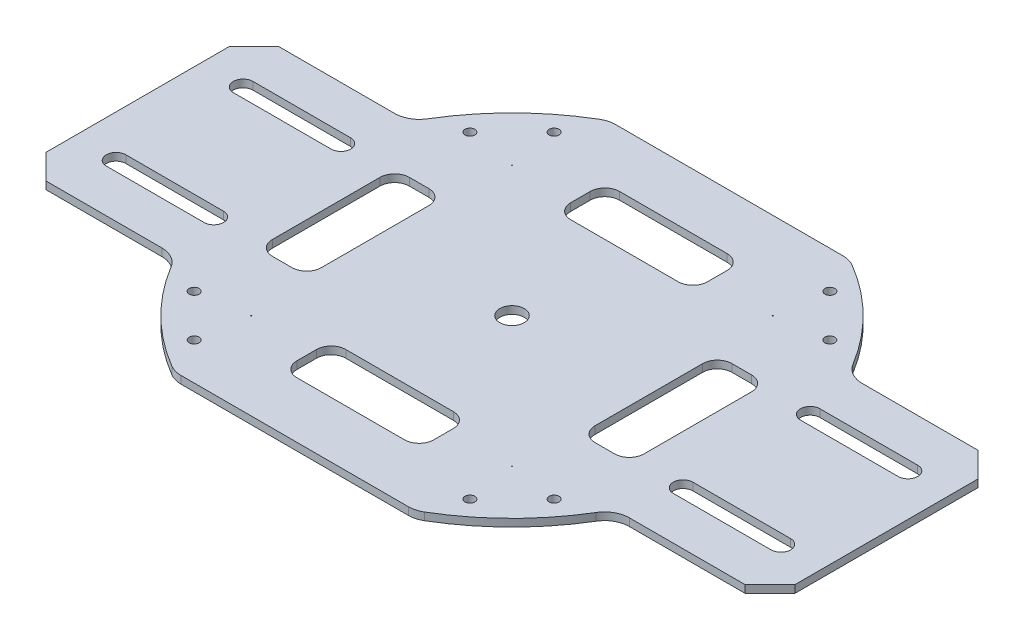
SolidWorks part; units mm, degrees
ref_plane "Front Plane" through (0, 0, 0) normal (0, 0, 1) x (1, 0, 0)
ref_plane "Top Plane" through (0, 0, 0) normal (0, 1, 0) x (1, 0, 0)
ref_plane "Right Plane" through (0, 0, 0) normal (1, 0, 0) x (0, 0, -1)
sketch "Sketch1" plane through (0, 0, 0) normal (0, 1, 0) x (1, 0, 0)
  line L0 (0, -1000) -> (0, 49000) construction
  line L1 (-23.2448, 44.45) -> (23.2448, 44.45)
  line L2 (-76.5969, 18.7325) -> (-76.5969, -18.7325)
  line L3 (-23.2448, -44.45) -> (23.2448, -44.45)
  line L4 (76.5969, 18.7325) -> (76.5969, -18.7325)
  line L6 (35.4178, 36.4243) -> (41.9684, 29.8736) construction
  line L7 (-76.5969, 0) -> (76.5969, 0) construction
  line L8 (-71.5169, 23.8125) -> (-47.8309, 23.8125)
  line L9 (-71.5169, -23.8125) -> (-47.8309, -23.8125)
  line L10 (-23.8125, 64.7529) -> (-23.8125, -44.45) construction
  line L11 (23.8125, 64.7529) -> (23.8125, -44.45) construction
  line L12 (47.8309, -23.8125) -> (71.5169, -23.8125)
  line L13 (47.8309, 23.8125) -> (71.5169, 23.8125)
  line L14 (-76.5969, -18.7325) -> (-71.5169, -23.8125)
  line L15 (-71.5169, 23.8125) -> (-76.5969, 18.7325)
  line L16 (71.5169, 23.8125) -> (76.5969, 18.7325)
  line L17 (71.5169, -23.8125) -> (76.5969, -18.7325)
  line L18 (707.1068, -707.1068) -> (-34648.2323, 34648.2323) construction
  line L19 (-707.1068, -707.1068) -> (34648.2323, 34648.2323) construction
  circle A0 centre (0, 0) radius 2.5
  arc A1 (-25.8276, 43.7444) -> (-43.4827, 26.2659) centre (0, 0) ccw
  arc A2 (25.8276, 43.7444) -> (23.2448, 44.45) centre (23.2448, 39.37) ccw
  arc A3 (-23.2448, 44.45) -> (-25.8276, 43.7444) centre (-23.2448, 39.37) ccw
  arc A4 (25.8276, -43.7444) -> (43.4827, -26.2659) centre (0, 0) ccw
  arc A5 (25.8276, -43.7444) -> (23.2448, -44.45) centre (23.2448, -39.37) cw
  arc A6 (-25.8276, -43.7444) -> (-23.2448, -44.45) centre (-23.2448, -39.37) ccw
  arc A7 (-43.4827, -26.2659) -> (-25.8276, -43.7444) centre (0, 0) ccw
  arc A8 (43.4827, 26.2659) -> (25.8276, 43.7444) centre (0, 0) ccw
  arc A9 (-47.8309, -23.8125) -> (-43.4827, -26.2659) centre (-47.8309, -28.8925) cw
  arc A10 (47.8309, -23.8125) -> (43.4827, -26.2659) centre (47.8309, -28.8925) ccw
  arc A11 (43.4827, 26.2659) -> (47.8309, 23.8125) centre (47.8309, 28.8925) ccw
  arc A12 (-47.8309, 23.8125) -> (-43.4827, 26.2659) centre (-47.8309, 28.8925) ccw
  circle A13 centre (36.8191, 28.198) radius 1.016
  circle A14 centre (28.198, 36.8191) radius 1.016
  circle A15 centre (26.6716, 26.6716) radius 0.081
  circle A16 centre (26.6716, -26.6716) radius 0.081
  circle A17 centre (36.8191, -28.198) radius 1.016
  circle A18 centre (28.198, -36.8191) radius 1.016
  circle A19 centre (-26.6716, -26.6716) radius 0.081
  circle A20 centre (-28.198, -36.8191) radius 1.016
  circle A21 centre (-36.8191, -28.198) radius 1.016
  circle A22 centre (-26.6716, 26.6716) radius 0.081
  circle A23 centre (-36.8191, 28.198) radius 1.016
  circle A24 centre (-28.198, 36.8191) radius 1.016
  point P0 (0, 0)
  point P8 (76.5969, -23.8125)
  point P11 (-76.5969, -23.8125)
  point P12 (-76.5969, 23.8125)
  point P34 (76.5969, 23.8125)
  point P81 (0, 0)
  dimension "D3" = 5
  dimension "D6" = 5.08
  dimension "D1" = 5.08
  dimension "D2" = 5.08
  dimension "D7" = 4.826
  dimension "D4" = 23.8125
  dimension "D5" = 23.8125
  dimension "D8" = 6.096
  dimension "D13" = 4
extrude "Boss-Extrude1" add sketch "Sketch1" along normal blind 1.55
sketch "Sketch2" plane through (0, 1.55, 0) normal (0, 1, 0) x (1, 0, 0)
  line L0 (-76.5969, 0) -> (76.5969, 0) construction
  line L1 (-76.5969, 18.7325) -> (-76.5969, -18.7325) construction
  line L2 (76.5969, -18.7325) -> (76.5969, 18.7325) construction
  line L3 (48, 13) -> (68, 13) construction
  line L4 (48, 15) -> (68, 15)
  line L5 (48, 11) -> (68, 11)
  line L6 (48, -13) -> (68, -13) construction
  line L7 (48, -15) -> (68, -15)
  line L8 (48, -11) -> (68, -11)
  line L9 (0, 44.45) -> (0, -44.45) construction
  line L10 (23.2448, 44.45) -> (-23.2448, 44.45) construction
  line L11 (-23.2448, -44.45) -> (23.2448, -44.45) construction
  line L12 (-48, 13) -> (-68, 13) construction
  line L13 (-48, 15) -> (-68, 15)
  line L14 (-48, 11) -> (-68, 11)
  line L15 (-48, -13) -> (-68, -13) construction
  line L16 (-48, -15) -> (-68, -15)
  line L17 (-48, -11) -> (-68, -11)
  arc A0 (48, 15) -> (48, 11) centre (48, 13) ccw
  arc A1 (68, 11) -> (68, 15) centre (68, 13) ccw
  arc A2 (48, -15) -> (48, -11) centre (48, -13) cw
  arc A3 (68, -11) -> (68, -15) centre (68, -13) cw
  arc A4 (-48, 15) -> (-48, 11) centre (-48, 13) cw
  arc A5 (-68, 11) -> (-68, 15) centre (-68, 13) cw
  arc A6 (-48, -15) -> (-48, -11) centre (-48, -13) ccw
  arc A7 (-68, -11) -> (-68, -15) centre (-68, -13) ccw
  point P8 (58, 13)
  point P15 (58, -13)
  point P20 (46, 13)
  point P21 (70, 13)
  point P28 (0, 0)
  point P29 (0, 0)
  point P30 (0, 0)
  point P33 (-58, 13)
  point P40 (-58, -13)
  dimension "D1" = 11
  dimension "D2" = 15
  dimension "D4" = 46
  dimension "D5" = 70
extrude "Cut-Extrude1" cut sketch "Sketch2" against normal through all
sketch "Sketch3" plane through (0, 1.55, 0) normal (0, 1, 0) x (1, 0, 0)
  line L0 (-76.5969, 0) -> (76.5969, 0) construction
  line L1 (-11, 33) -> (11, 33)
  line L2 (-14, 30) -> (-14, 26)
  line L3 (-11, 23) -> (11, 23)
  line L4 (14, 30) -> (14, 26)
  line L5 (-76.5969, 18.7325) -> (-76.5969, -18.7325) construction
  line L6 (76.5969, -18.7325) -> (76.5969, 18.7325) construction
  line L7 (0, 44.45) -> (0, -44.45) construction
  line L8 (23.2448, 44.45) -> (-23.2448, 44.45) construction
  line L9 (-23.2448, -44.45) -> (23.2448, -44.45) construction
  line L10 (14, -30) -> (14, -26)
  line L11 (-11, -23) -> (11, -23)
  line L12 (-14, -30) -> (-14, -26)
  line L13 (-11, -33) -> (11, -33)
  line L14 (-28, -14) -> (-38, 14) construction
  line L15 (31, 14) -> (35, 14)
  line L16 (28, 11) -> (28, -11)
  line L17 (31, -14) -> (35, -14)
  line L18 (38, 11) -> (38, -11)
  line L19 (28, 14) -> (38, -14) construction
  line L20 (28, -14) -> (38, 14) construction
  line L21 (-28, 14) -> (-38, -14) construction
  line L22 (-38, 11) -> (-38, -11)
  line L23 (-31, -14) -> (-35, -14)
  line L24 (-28, 11) -> (-28, -11)
  line L25 (-31, 14) -> (-35, 14)
  arc A0 (-11, 33) -> (-14, 30) centre (-11, 30) ccw
  arc A1 (-14, 26) -> (-11, 23) centre (-11, 26) ccw
  arc A2 (11, 23) -> (14, 26) centre (11, 26) ccw
  arc A3 (11, 33) -> (14, 30) centre (11, 30) cw
  arc A4 (11, -33) -> (14, -30) centre (11, -30) ccw
  arc A5 (11, -23) -> (14, -26) centre (11, -26) cw
  arc A6 (-14, -26) -> (-11, -23) centre (-11, -26) cw
  arc A7 (-11, -33) -> (-14, -30) centre (-11, -30) cw
  arc A8 (35, -14) -> (38, -11) centre (35, -11) ccw
  arc A9 (28, -11) -> (31, -14) centre (31, -11) ccw
  arc A10 (31, 14) -> (28, 11) centre (31, 11) ccw
  arc A11 (35, 14) -> (38, 11) centre (35, 11) cw
  arc A12 (-35, 14) -> (-38, 11) centre (-35, 11) ccw
  arc A13 (-31, 14) -> (-28, 11) centre (-31, 11) cw
  arc A14 (-28, -11) -> (-31, -14) centre (-31, -11) cw
  arc A15 (-35, -14) -> (-38, -11) centre (-35, -11) cw
  point P36 (33, 0)
  point P69 (-33, 0)
  dimension "D5" = 3
  dimension "D9" = 3
  dimension "D1" = 23
  dimension "D2" = 33
  dimension "D3" = 28
  dimension "D4" = 14
  dimension "D6" = 28
  dimension "D7" = 38
  dimension "D8" = 28
extrude "Cut-Extrude2" cut sketch "Sketch3" against normal through all
